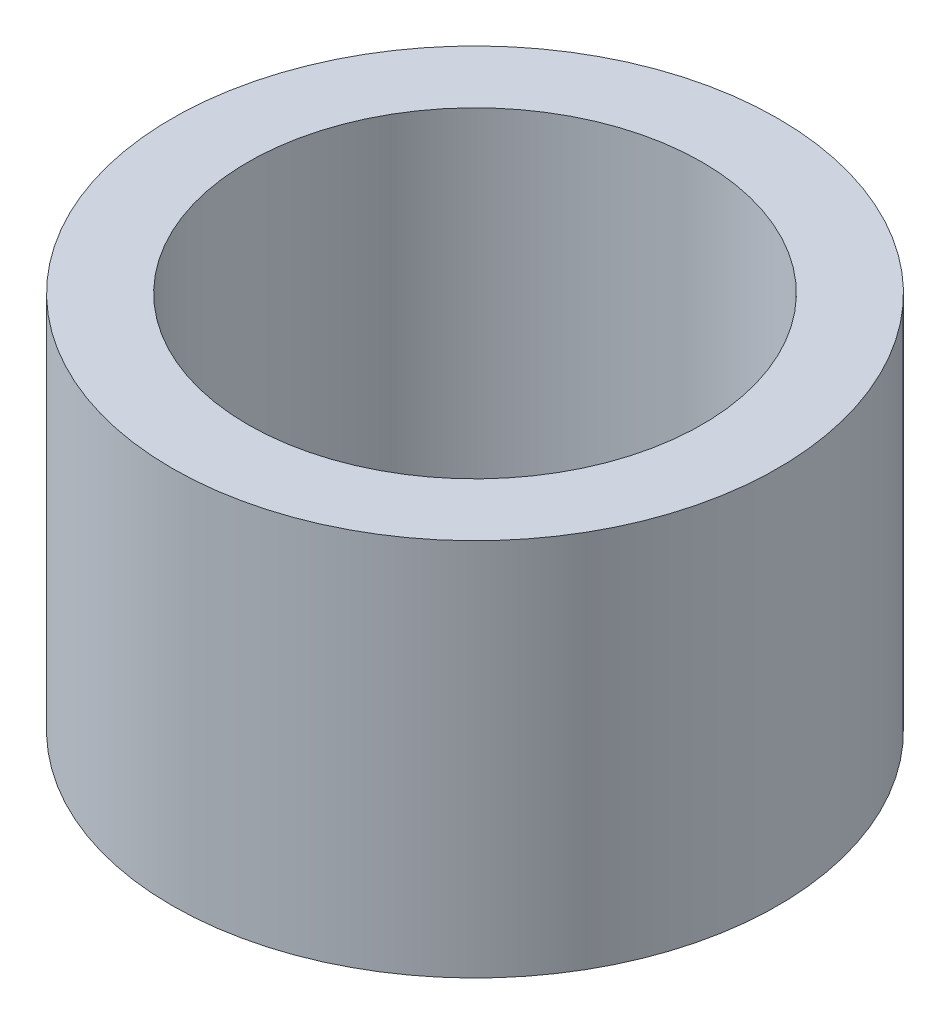
SolidWorks part; units mm, degrees
material "ｽﾃﾝﾚｽ鋼(ｸﾛﾑ)"
ref_plane "正面" through (0, 0, 0) normal (0, 0, 1) x (1, 0, 0)
ref_plane "平面" through (0, 0, 0) normal (0, 1, 0) x (1, 0, 0)
ref_plane "右側面" through (0, 0, 0) normal (1, 0, 0) x (0, 0, -1)
sketch "ｽｹｯﾁ1" plane through (0, 0, 0) normal (0, 1, 0) x (1, 0, 0)
  circle A0 centre (0, 0) radius 6
  circle A1 centre (0, 0) radius 8
  dimension "D1" = 12
  dimension "D2" = 16
extrude "ﾎﾞｽ - 押し出し1" add sketch "ｽｹｯﾁ1" along normal blind 10
